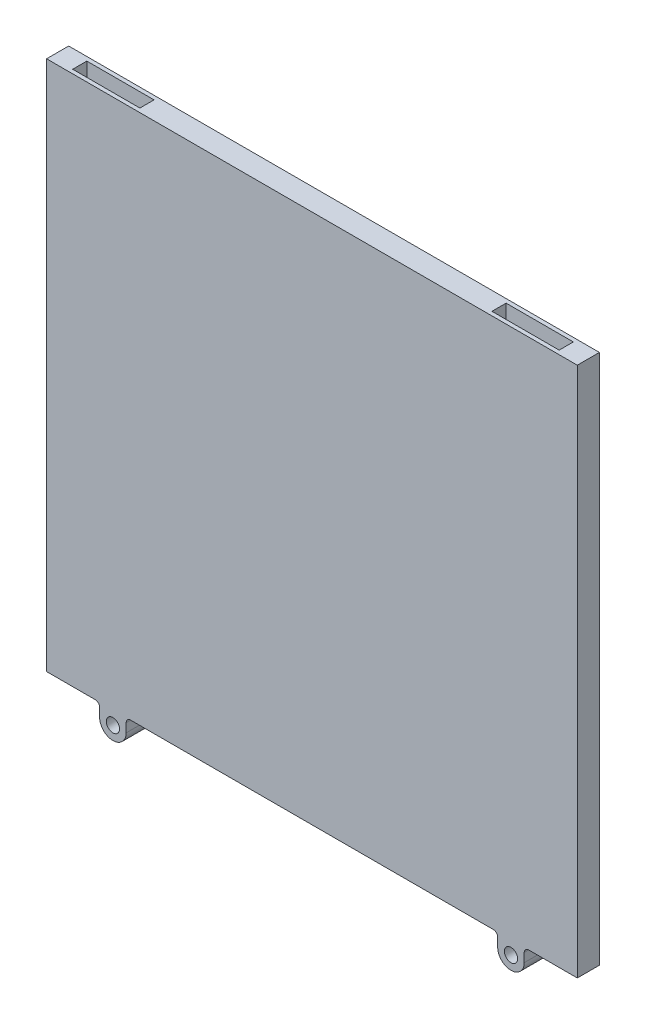
SolidWorks part; units mm, degrees
ref_plane "Front Plane" through (0, 0, 0) normal (0, 0, 1) x (1, 0, 0)
ref_plane "Top Plane" through (0, 0, 0) normal (0, 1, 0) x (1, 0, 0)
ref_plane "Right Plane" through (0, 0, 0) normal (1, 0, 0) x (0, 0, -1)
sketch "Sketch1" plane through (0, 0, 0) normal (0, 0, 1) x (1, 0, 0)
  line L1 (60, -60) -> (-60, -60)
  line L2 (60, -60) -> (60, 60)
  line L3 (60, 60) -> (-60, 60)
  line L4 (-60, -60) -> (-60, 60)
  line L5 (60, -60) -> (-60, 60) construction
  line L6 (60, 60) -> (-60, -60) construction
  point P0 (0, 0)
  dimension "D1" = 120
  dimension "D2" = 120
extrude "Boss-Extrude1" add sketch "Sketch1" along normal mid plane 5 contours L2 L3 L4 L1
sketch "Sketch4" plane through (0, 60, 0) normal (0, 1, 0) x (1, 0, 0)
  line L0 (-60, 0) -> (60, 0) construction
  line L1 (-55, -1.6) -> (-39.8, -1.6)
  line L2 (-55, -1.6) -> (-55, 1.6)
  line L3 (-55, 1.6) -> (-39.8, 1.6)
  line L4 (-39.8, -1.6) -> (-39.8, 1.6)
  line L5 (-55, -1.6) -> (-39.8, 1.6) construction
  line L6 (-55, 1.6) -> (-39.8, -1.6) construction
  line L7 (-60, -2.5) -> (-60, 2.5) construction
  line L8 (60, -2.5) -> (60, 2.5) construction
  line L9 (0, -2.75) -> (0, 2.75) construction
  line L10 (55, -1.6) -> (39.8, -1.6)
  line L11 (39.8, -1.6) -> (39.8, 1.6)
  line L12 (55, 1.6) -> (39.8, 1.6)
  line L13 (55, -1.6) -> (55, 1.6)
  point P0 (-47.4, 0)
  dimension "D1" = 15.2
  dimension "D2" = 3.2
  dimension "D3" = 5
extrude "Cut-Extrude1" cut sketch "Sketch4" against normal blind 20
sketch "Sketch7" plane through (0, -60, 0) normal (0, -1, 0) x (1, 0, 0)
  line L0 (66, 0) -> (-66, 0) construction
  line L1 (-41.75, -1.6) -> (-48.25, -1.6)
  line L2 (-41.75, -1.6) -> (-41.75, 1.6)
  line L3 (-41.75, 1.6) -> (-48.25, 1.6)
  line L4 (-48.25, -1.6) -> (-48.25, 1.6)
  line L5 (-41.75, -1.6) -> (-48.25, 1.6) construction
  line L6 (-41.75, 1.6) -> (-48.25, -1.6) construction
  line L7 (-60, 2.5) -> (-60, -2.5) construction
  point P0 (-45, 0)
  dimension "D1" = 11.75
  dimension "D2" = 6.5
  dimension "D3" = 3.2
extrude "Cut-Extrude2" [suppressed] cut sketch "Sketch7" against normal blind 12
mirror "Mirror2" [suppressed] about plane through (0, 0, 0) normal (1, 0, 0)
sketch "Sketch6" plane through (0, 0, 2.5) normal (0, 0, 1) x (1, 0, 0)
  line L0 (60, -60) -> (-60, -60) construction
  line L1 (42, -60) -> (48, -60)
  line L5 (60, -60) -> (60, 60) construction
  line L6 (42, -60) -> (42, -63)
  line L8 (48, -63) -> (48, -60)
  line L9 (45, -60) -> (45, -66) construction
  circle A1 centre (45, -63) radius 1.5
  arc A2 (42, -63) -> (48, -63) centre (45, -63) ccw
  point P12 (0, 0)
  dimension "D2" = 3
  dimension "D4" = 3
  dimension "D1" = 6
  dimension "D3" = 15
extrude "Boss-Extrude2" add sketch "Sketch6" against normal up to surface (5 mm away) up to face at (0, 0, -2.5)
fillet "Fillet1" radius 1 2 edges at (48, -60, 0) (42, -60, 0)
mirror "Mirror1" about plane through (0, 0, 0) normal (1, 0, 0) of "Fillet1", "Boss-Extrude2"
